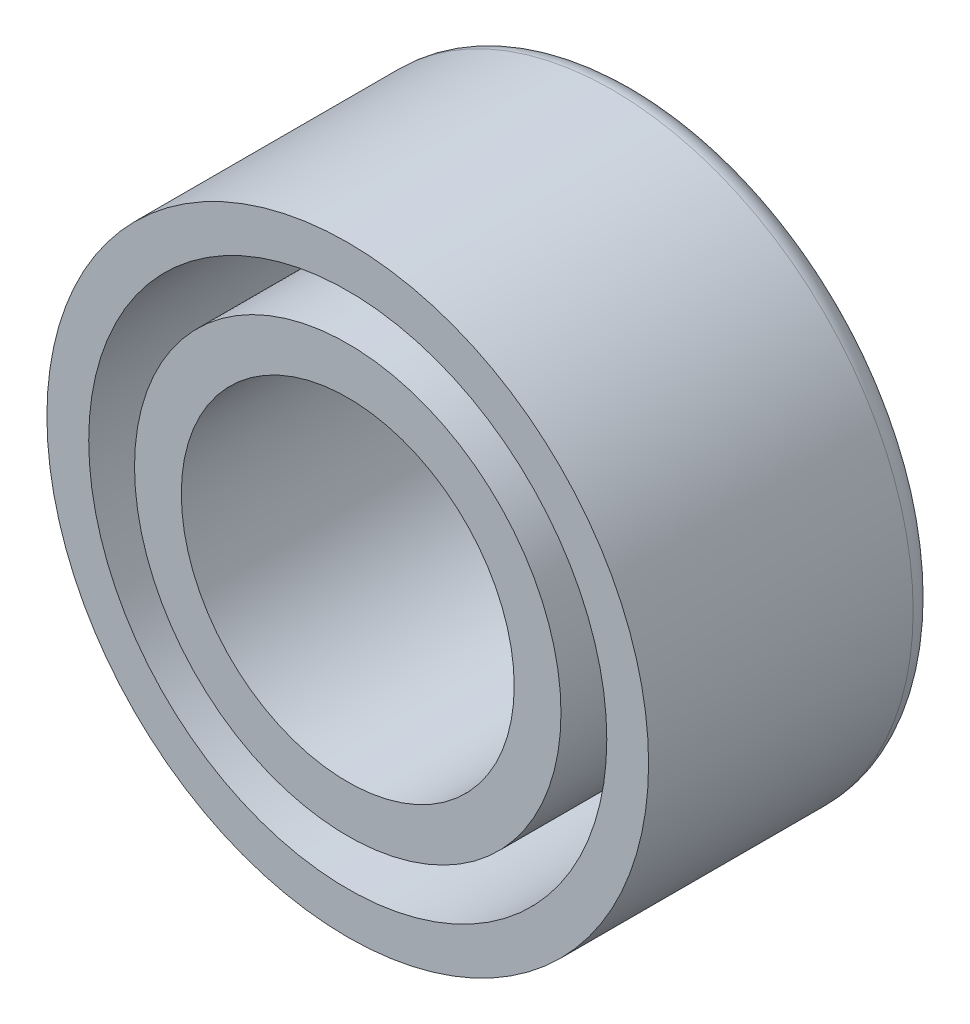
SolidWorks part; units mm, degrees
ref_plane "Front Plane" through (0, 0, 0) normal (0, 0, 1) x (1, 0, 0)
ref_plane "Top Plane" through (0, 0, 0) normal (0, 1, 0) x (1, 0, 0)
ref_plane "Right Plane" through (0, 0, 0) normal (1, 0, 0) x (0, 0, -1)
sketch "Sketch1" plane through (0, 0, 0) normal (0, 0, 1) x (1, 0, 0)
  circle A0 centre (0, 0) radius 6.9215
  circle A1 centre (0, 0) radius 12.5095
  dimension "D1" = 13.843
  dimension "D2" = 5.588
extrude "Boss-Extrude1" add sketch "Sketch1" along normal blind 12
fillet "Fillet1" radius 1 2 edges at (6.9215, 0, 0) (12.5095, 0, 0)
sketch "Sketch2" plane through (0, 0, 12) normal (0, 0, 1) x (1, 0, 0)
  circle A0 centre (0, 0) radius 10.7715
  circle A1 centre (0, 0) radius 6.9215 construction
  circle A2 centre (0, 0) radius 8.8665
  dimension "D1" = 3.85
  dimension "D2" = 1.905
extrude "Cut-Extrude1" cut sketch "Sketch2" against normal blind 9
